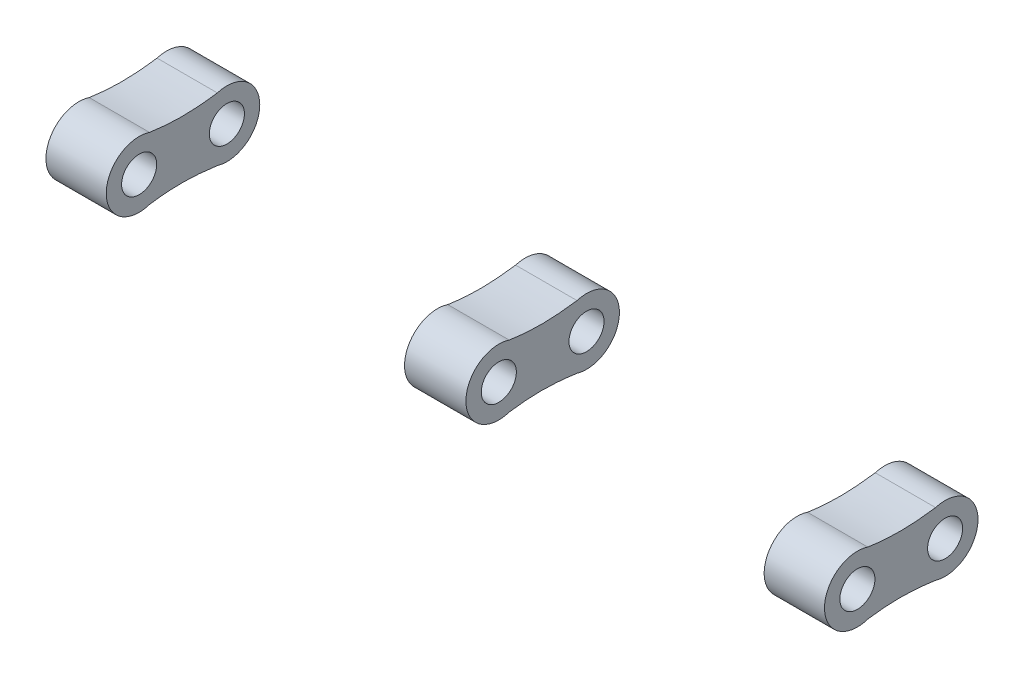
SolidWorks part; units mm, degrees
ref_plane "Plano frontal" through (0, 0, 0) normal (0, 0, 1) x (1, 0, 0)
ref_plane "Plano superior" through (0, 0, 0) normal (0, 1, 0) x (1, 0, 0)
ref_plane "Plano direito" through (0, 0, 0) normal (1, 0, 0) x (0, 0, -1)
sketch "Esboço1" plane through (8.875, 0, 0) normal (1, 0, 0) x (0, 0, -1)
  circle A0 centre (1.5, 0) radius 0.4
  circle A1 centre (3.5, 0) radius 0.4
  arc A2 (1.7376, 0.7114) -> (1.7376, -0.7114) centre (1.5, 0) ccw
  arc A3 (3.2832, -0.718) -> (3.2832, 0.718) centre (3.5, 0) ccw
  spline S0 degree 3 poles (1.7376, 0.7114) (2.3047, 0.6286) (2.7257, 0.6409) (3.2832, 0.718) knots 0.106827 0.106827 0.106827 0.106827 0.900451 0.900451 0.900451 0.900451
  spline S1 degree 3 poles (1.7376, -0.7114) (2.3047, -0.6286) (2.7257, -0.6409) (3.2832, -0.718) knots 0.106827 0.106827 0.106827 0.106827 0.900451 0.900451 0.900451 0.900451
extrude "Ressalto-extrusão1" add sketch "Esboço1" against normal up to surface (1.375 mm away)
sketch "Esboço2" plane through (-7.5, 0, 0) normal (-1, 0, 0) x (0, 0, 1)
  circle A1 centre (-3.5, 0) radius 0.4
  arc A2 (-1.7376, -0.7114) -> (-1.7376, 0.7114) centre (-1.5, 0) ccw
  arc A3 (-3.2832, 0.718) -> (-3.2832, -0.718) centre (-3.5, 0) ccw
  arc A4 (-1.7376, -0.7114) -> (-1.7376, 0.7114) centre (-1.5, 0) ccw
  arc A5 (-3.2832, 0.718) -> (-3.2832, -0.718) centre (-3.5, 0) ccw
  circle A6 centre (-3.5, 0) radius 0.4
  circle A7 centre (-1.5, 0) radius 0.4
  circle A8 centre (-1.5, 0) radius 0.4
  spline S2 degree 3 poles (-2996.1228, 200.5163) (2940.1549, -277.8811) (-2937.5023, 351.5733) (2967.5108, -426.8401) knots -16.875771 -16.875771 -16.875771 -16.875771 17.810123 17.810123 17.810123 17.810123 only from (-3.2832, -0.718) to (-1.7376, -0.7114)
  spline S3 degree 3 poles (2967.6159, 426.854) (-2937.5795, -351.5818) (2940.205, 277.8855) (-2996.1453, -200.5181) knots -16.803051 -16.803051 -16.803051 -16.803051 17.883093 17.883093 17.883093 17.883093 only from (-1.7376, 0.7114) to (-3.2832, 0.718)
  spline S4 degree 3 poles (-3.2832, -0.718) (-2.7257, -0.6409) (-2.3047, -0.6286) (-1.7376, -0.7114) knots 0.106827 0.106827 0.106827 0.106827 0.900451 0.900451 0.900451 0.900451
  spline S5 degree 3 poles (-1.7376, 0.7114) (-2.3047, 0.6286) (-2.7257, 0.6409) (-3.2832, 0.718) knots 0.106827 0.106827 0.106827 0.106827 0.900451 0.900451 0.900451 0.900451
  dimension "D1" = 0
  dimension "D2" = 0
  dimension "D3" = 0
extrude "Ressalto-extrusão2" add sketch "Esboço2" along normal up to surface (1.375 mm away) separate body
sketch "Esboço3" plane through (-0.7, 0, 0) normal (1, 0, 0) x (0, 0, -1)
  circle A1 centre (3.5, 0) radius 0.4
  arc A2 (1.7376, 0.7114) -> (1.7376, -0.7114) centre (1.5, 0) ccw
  arc A3 (3.2832, -0.718) -> (3.2832, 0.718) centre (3.5, 0) ccw
  arc A4 (1.7376, 0.7114) -> (1.7376, -0.7114) centre (1.5, 0) ccw
  arc A5 (3.2832, -0.718) -> (3.2832, 0.718) centre (3.5, 0) ccw
  circle A6 centre (3.5, 0) radius 0.4
  circle A7 centre (1.5, 0) radius 0.4
  circle A8 centre (1.5, 0) radius 0.4
  spline S2 degree 3 poles (-2967.6159, -426.854) (2937.5795, 351.5818) (-2940.205, -277.8855) (2996.1453, 200.5181) knots -16.803051 -16.803051 -16.803051 -16.803051 17.883093 17.883093 17.883093 17.883093 only from (1.7376, -0.7114) to (3.2832, -0.718)
  spline S3 degree 3 poles (2996.1228, -200.5163) (-2940.1549, 277.8811) (2937.5023, -351.5733) (-2967.5108, 426.8401) knots -16.875771 -16.875771 -16.875771 -16.875771 17.810123 17.810123 17.810123 17.810123 only from (3.2832, 0.718) to (1.7376, 0.7114)
  spline S4 degree 3 poles (1.7376, -0.7114) (2.3047, -0.6286) (2.7257, -0.6409) (3.2832, -0.718) knots 0.106827 0.106827 0.106827 0.106827 0.900451 0.900451 0.900451 0.900451
  spline S5 degree 3 poles (3.2832, 0.718) (2.7257, 0.6409) (2.3047, 0.6286) (1.7376, 0.7114) knots 0.106827 0.106827 0.106827 0.106827 0.900451 0.900451 0.900451 0.900451
  dimension "D1" = 0
  dimension "D2" = 0
  dimension "D3" = 0
extrude "Ressalto-extrusão3" add sketch "Esboço3" along normal up to surface (1.4 mm away) separate body
